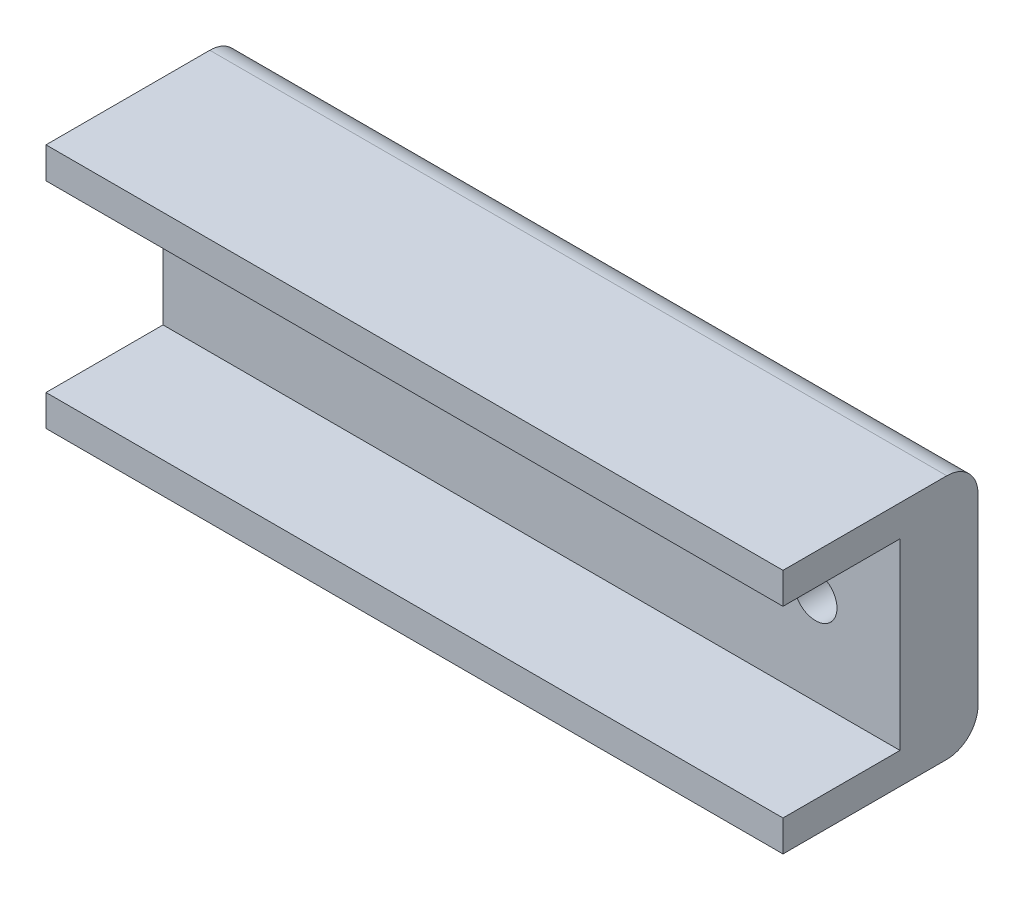
SolidWorks part; units mm, degrees
ref_plane "Front Plane" through (0, 0, 0) normal (0, 0, 1) x (1, 0, 0)
ref_plane "Top Plane" through (0, 0, 0) normal (0, 1, 0) x (1, 0, 0)
ref_plane "Right Plane" through (0, 0, 0) normal (1, 0, 0) x (0, 0, -1)
sketch "Sketch1" plane through (0, 0, 0) normal (0, 0, 1) x (1, 0, 0)
  line L0 (-30, 0) -> (30, 0) construction
  line L1 (30, -10) -> (-30, -10)
  line L2 (30, -10) -> (30, 10)
  line L3 (30, 10) -> (-30, 10)
  line L4 (-30, -10) -> (-30, 10)
  line L5 (30, -10) -> (-30, 10) construction
  line L6 (30, 10) -> (-30, -10) construction
  circle A0 centre (-23.12, 0) radius 1.75
  circle A1 centre (23.12, 0) radius 1.75
  point P0 (0, 0)
  dimension "D3" = 3.5
  dimension "D4" = 3.5
  dimension "D1" = 20
  dimension "D2" = 60
  dimension "D5" = 46.24
  dimension "D6" = 23.12
extrude "Boss-Extrude1" add sketch "Sketch1" along normal blind 6.35
sketch "Sketch2" plane through (0, 0, 6.35) normal (0, 0, 1) x (1, 0, 0)
  line L0 (30, -10) -> (30, 10) construction
  line L1 (-30, 10) -> (30, 10)
  line L2 (-30, 10) -> (-30, 7.46)
  line L3 (-30, 7.46) -> (30, 7.46)
  line L4 (30, 10) -> (30, 7.46)
  line L6 (-30, -10) -> (30, -10)
  line L7 (-30, -10) -> (-30, -7.46)
  line L8 (-30, -7.46) -> (30, -7.46)
  line L9 (30, -10) -> (30, -7.46)
  dimension "D1" = 2.54
  dimension "D2" = 2.54
extrude "Boss-Extrude2" add sketch "Sketch2" along normal blind 9.525
fillet "Fillet1" radius 2.54 2 edges at (0, 10, 0) (0, -10, 0)
